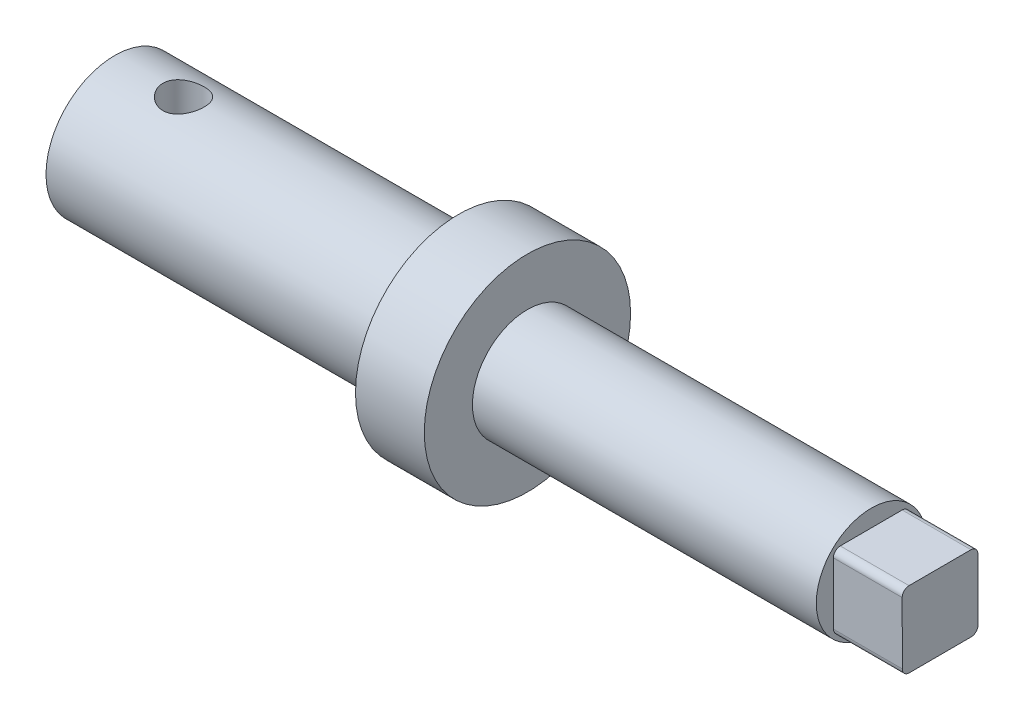
SolidWorks part; units mm, degrees
ref_plane "前视基准面" through (0, 0, 0) normal (0, 0, 1) x (1, 0, 0)
ref_plane "上视基准面" through (0, 0, 0) normal (0, 1, 0) x (1, 0, 0)
ref_plane "右视基准面" through (0, 0, 0) normal (1, 0, 0) x (0, 0, -1)
sketch "草图1" plane through (0, 0, 0) normal (0, 0, 1) x (1, 0, 0)
  line L0 (0, 0) -> (46.7995, 0) construction
  line L1 (0, 0) -> (0, 5)
  line L2 (0, 5) -> (25, 5)
  line L3 (25, 5) -> (25, 7.5)
  line L4 (25, 7.5) -> (30, 7.5)
  line L5 (30, 7.5) -> (30, 4)
  line L6 (30, 4) -> (55, 4)
  line L7 (55, 4) -> (55, 0)
  line L8 (55, 0) -> (0, 0)
  dimension "D1" = 10
  dimension "D2" = 15
  dimension "D3" = 8
  dimension "D4" = 25
  dimension "D5" = 5
  dimension "D6" = 25
revolve "旋转1" add sketch "草图1" angle 360 about L0
sketch "草图2" plane through (0, 0, 0) normal (0, 1, 0) x (1, 0, 0)
  line L0 (0, 0) -> (5, 0) construction
  circle A0 centre (5, 0) radius 1.5
  dimension "D2" = 3
  dimension "D1" = 5
extrude "切除-拉伸1" cut sketch "草图2" against normal mid plane 10
sketch "草图3" plane through (55, 0, 0) normal (1, 0, 0) x (0, 0, -1)
  line L1 (-2.7573, 2.7427) -> (-2.7427, -2.7573)
  line L2 (-2.7427, -2.7573) -> (2.7573, -2.7427)
  line L3 (2.7573, -2.7427) -> (2.7427, 2.7573)
  line L4 (2.7427, 2.7573) -> (-2.7573, 2.7427)
  circle A0 centre (0, 0) radius 2.75 construction
  dimension "D2" = 5.5
  dimension "D1" = 5.5
extrude "凸台-拉伸1" add sketch "草图3" along normal blind 5 contours L1 L2 L3 L4
fillet "圆角1" radius 0.5 4 edges at (57.5, 2.7573, -2.7427) (57.5, -2.7427, -2.7573) (57.5, -2.7573, 2.7427) (57.5, 2.7427, 2.7573)
